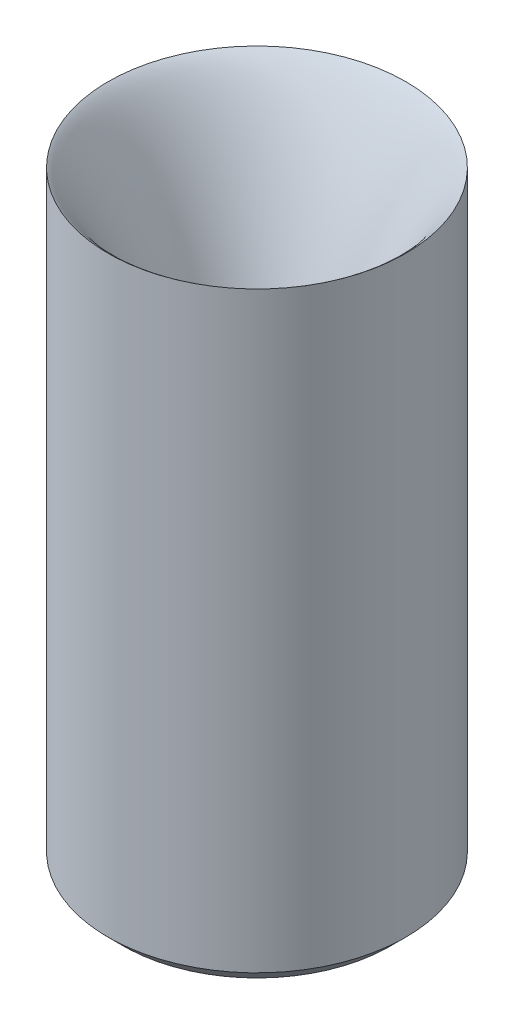
SolidWorks part; units mm, degrees
ref_plane "Спереди" through (0, 0, 0) normal (0, 0, 1) x (1, 0, 0)
ref_plane "Сверху" through (0, 0, 0) normal (0, 1, 0) x (1, 0, 0)
ref_plane "Справа" through (0, 0, 0) normal (1, 0, 0) x (0, 0, -1)
sketch "Эскиз1" plane through (0, 0, 0) normal (0, 0, 1) x (1, 0, 0)
  line L0 (0, 0) -> (0, 7.9558) construction
  line L1 (1.5, 0) -> (9.8, 0)
  line L2 (9.8, 0) -> (9.8, 40)
  line L4 (0.9, 4.1689) -> (0.9, 5.5757) construction
  line L5 (0.9, 11) -> (0.9, 8)
  line L6 (0.9, 8) -> (1.5, 8)
  line L7 (1.5, 8) -> (1.5, 0)
  spline S0 degree 3 poles (9.8, 40) (7.4539, 38.4345) (0.9, 22) (0.9, 11) knots 0 0 0 0 1 1 1 1
  dimension "D6" = 40
  dimension "D7" = 33
  dimension "D1" = 3
  dimension "D2" = 19.6
  dimension "D3" = 1.8
  dimension "D4" = 3
  dimension "D5" = 8
revolve "Повернуть1" add sketch "Эскиз1" angle 360 about L0
chamfer "Фаска1" distance 1 angle 45 2 edges at (0, 0, -9.8) (0, 0, -1.5)
